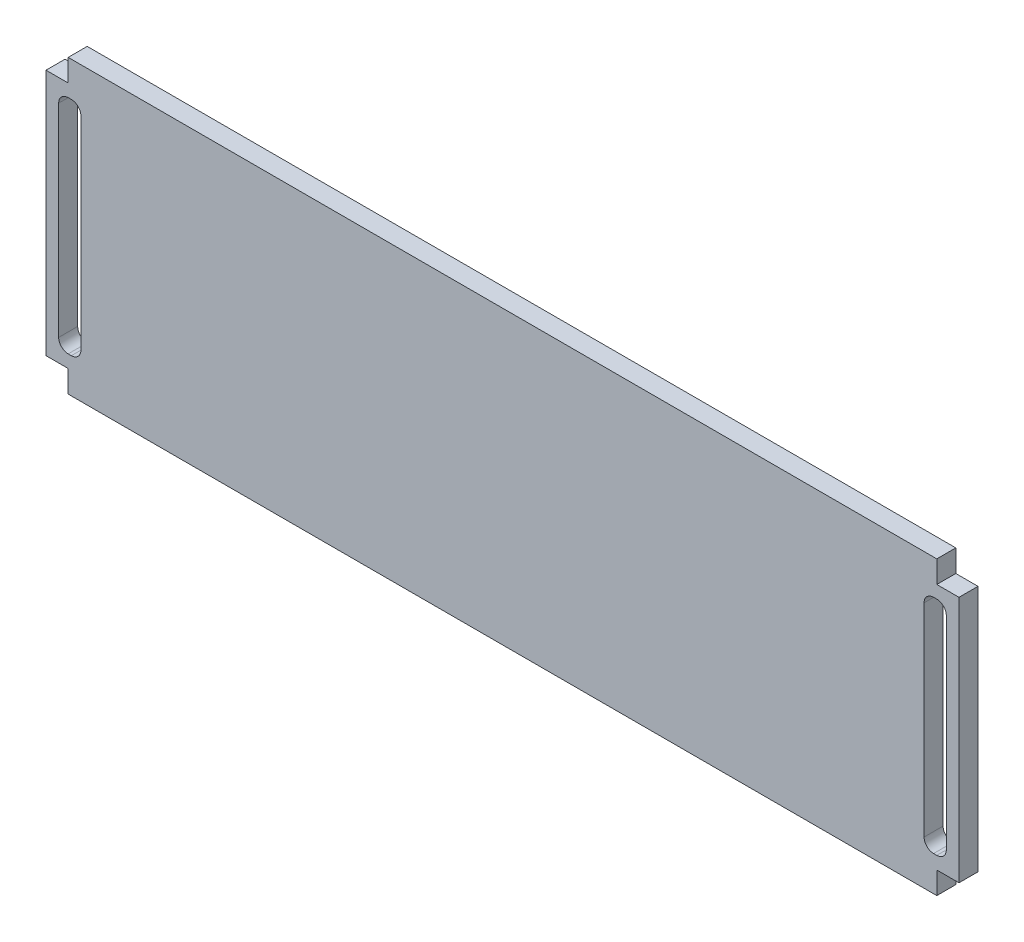
SolidWorks part; units mm, degrees
material "ABS PC"
ref_plane "Front Plane" through (0, 0, 0) normal (0, 0, 1) x (1, 0, 0)
ref_plane "Top Plane" through (0, 0, 0) normal (0, 1, 0) x (1, 0, 0)
ref_plane "Right Plane" through (0, 0, 0) normal (1, 0, 0) x (0, 0, -1)
sketch "Sketch1" plane through (0, 0, 0) normal (0, 0, 1) x (1, 0, 0)
  line L0 (0, 0) -> (0, 46) construction
  line L1 (68.5, 46) -> (-68.5, 46)
  line L2 (-68.5, 46) -> (-68.5, 42.5)
  line L3 (-68.5, 42.5) -> (-72, 42.5)
  line L4 (-72, 42.5) -> (-72, 3.5)
  line L5 (-72, 3.5) -> (-68.5, 3.5)
  line L6 (-68.5, 3.5) -> (-68.5, 0)
  line L7 (-68.5, 0) -> (68.5, 0)
  line L8 (68.5, 3.5) -> (68.5, 0)
  line L9 (72, 3.5) -> (68.5, 3.5)
  line L10 (68.5, 46) -> (68.5, 42.5)
  line L11 (68.5, 42.5) -> (72, 42.5)
  line L12 (72, 42.5) -> (72, 3.5)
  dimension "D1" = 72
  dimension "D2" = 3.5
  dimension "D3" = 46
extrude "Boss-Extrude1" add sketch "Sketch1" along normal blind 3
sketch "Sketch2" plane through (0, 0, 3) normal (0, 0, 1) x (1, 0, 0)
  line L24 (-66.5, 40.5) -> (-66.5, 5.5)
  line L25 (66.5, 40.5) -> (66.5, 5.5)
  line L36 (66.5, 5.5) -> (70, 5.5)
  line L37 (70, 5.5) -> (70, 40.5)
  line L38 (70, 40.5) -> (66.5, 40.5)
  line L39 (66.5, 40.5) -> (66.5, 44)
  line L40 (66.5, 44) -> (-66.5, 44)
  line L41 (-66.5, 44) -> (-66.5, 40.5)
  line L42 (-66.5, 40.5) -> (-70, 40.5)
  line L43 (-70, 40.5) -> (-70, 5.5)
  line L44 (-70, 5.5) -> (-66.5, 5.5)
  line L45 (-66.5, 5.5) -> (-66.5, 2)
  line L46 (-66.5, 2) -> (66.5, 2)
  line L47 (66.5, 2) -> (66.5, 5.5)
  line L48 (66.5, 5.5) -> (70, 5.5)
  line L49 (70, 5.5) -> (70, 40.5)
  line L50 (70, 40.5) -> (66.5, 40.5)
  line L51 (66.5, 40.5) -> (66.5, 44)
  line L52 (66.5, 44) -> (-66.5, 44)
  line L53 (-66.5, 44) -> (-66.5, 40.5)
  line L54 (-66.5, 40.5) -> (-70, 40.5)
  line L55 (-70, 40.5) -> (-70, 5.5)
  line L56 (-70, 5.5) -> (-66.5, 5.5)
  line L57 (-66.5, 5.5) -> (-66.5, 2)
  line L58 (-66.5, 2) -> (66.5, 2)
  line L59 (66.5, 2) -> (66.5, 5.5)
  dimension "D1" = 2
extrude "Cut-Extrude7" cut sketch "Sketch2" against normal up to surface (3 mm away) contours L55 L56 L24 L54 | L49 L50 L25 L48 up to face at (0, 23, 0)
fillet "Fillet5" radius 1.5 8 edges at (-66.5, 5.5, 1.5) (-70, 5.5, 1.5) (-66.5, 40.5, 1.5) (-70, 40.5, 1.5) (70, 5.5, 1.5) (66.5, 5.5, 1.5) (66.5, 40.5, 1.5) (70, 40.5, 1.5)
